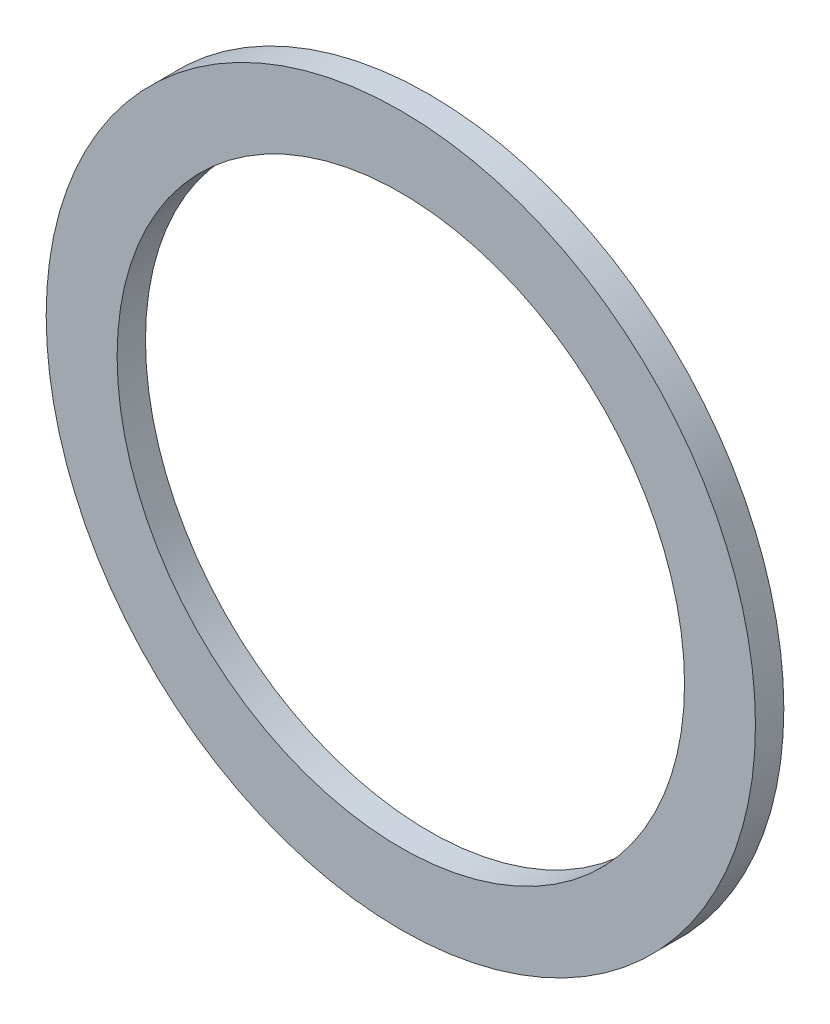
SolidWorks part; units mm, degrees
ref_plane "Front" through (0, 0, 0) normal (0, 0, 1) x (1, 0, 0)
ref_plane "Top" through (0, 0, 0) normal (0, 1, 0) x (1, 0, 0)
ref_plane "Right" through (0, 0, 0) normal (1, 0, 0) x (0, 0, -1)
sketch "Эскиз2" plane through (0, 0, 0) normal (0, 1, 0) x (1, 0, 0)
  line L0 (0, 0) -> (0, 20.7044) construction
  line L1 (-40, 0) -> (-50, 0)
  line L2 (-50, 0) -> (-50, 4)
  line L3 (-50, 4) -> (-40, 4)
  line L4 (-40, 4) -> (-40, 0)
  circle A0 centre (-45, 5.5) radius 3
  dimension "D1" = 6
  dimension "D2" = 50
  dimension "D3" = 45
  dimension "D4" = 40
  dimension "D5" = 4
  dimension "D6" = 1.5
revolve "Повернуть1" add sketch "Эскиз2" angle 360 about L0
